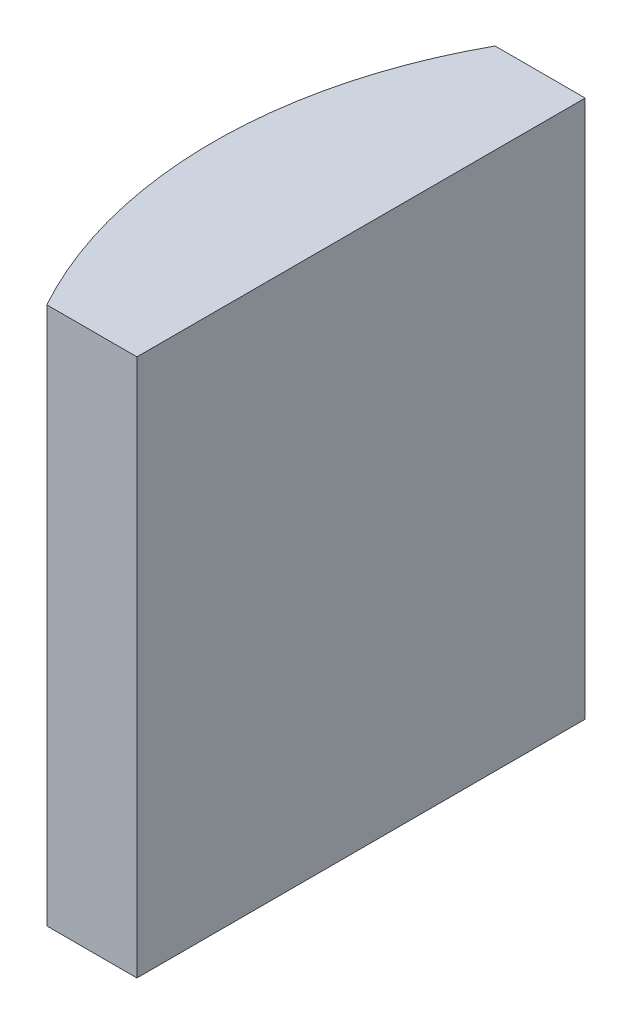
SolidWorks part; units mm, degrees
ref_plane "前视基准面" through (0, 0, 0) normal (0, 0, 1) x (1, 0, 0)
ref_plane "上视基准面" through (0, 0, 0) normal (0, 1, 0) x (1, 0, 0)
ref_plane "右视基准面" through (0, 0, 0) normal (1, 0, 0) x (0, 0, -1)
sketch "草图1" plane through (0, 0, 0) normal (0, 1, 0) x (1, 0, 0)
  line L0 (10.7432, 0) -> (-9.7696, 0) construction
  line L1 (-4.6955, 5) -> (-2.6848, 5)
  line L2 (-4.6955, -5) -> (-2.6848, -5)
  line L3 (-2.6848, 5) -> (-2.6848, -5)
  arc A0 (-4.6955, 5) -> (-4.6955, -5) centre (4.3552, 0) ccw
  point P19 (-5.9848, 0)
  point P20 (-2.6848, 0)
  dimension "D2" = 5
  dimension "D3" = 10.34
  dimension "D4" = 3.3
  dimension "D1" = 5
extrude "凸台-拉伸1" add sketch "草图1" along normal blind 12
